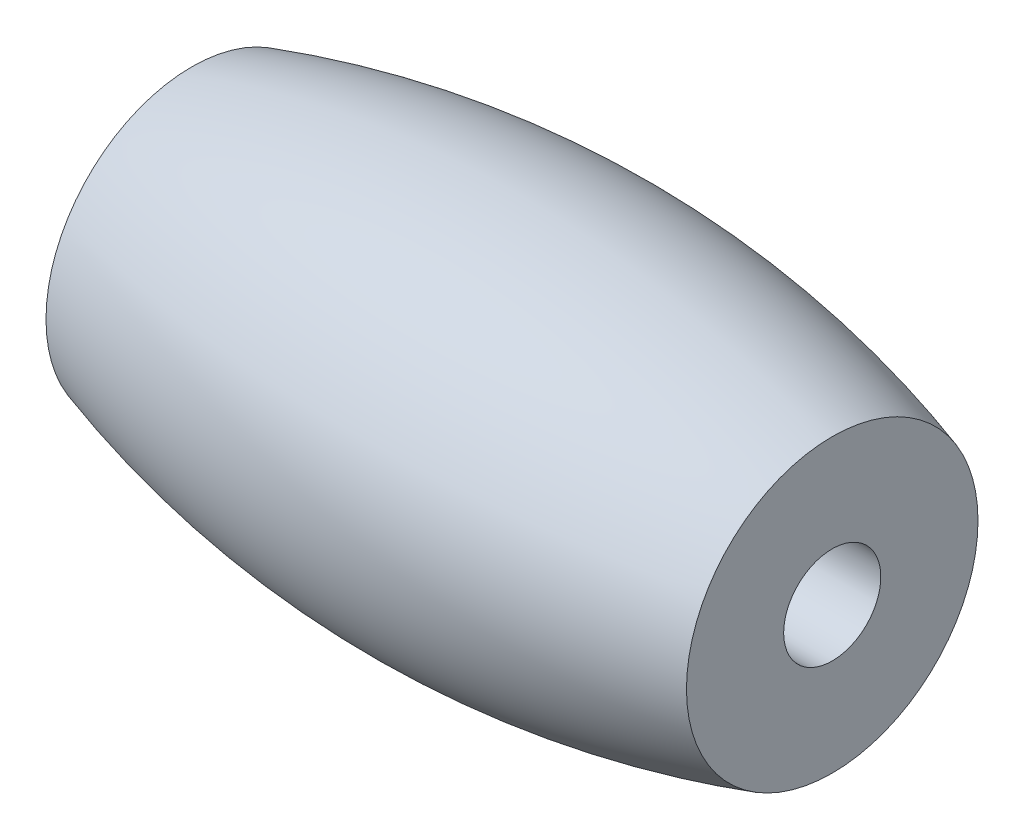
SolidWorks part; units mm, degrees
ref_plane "Front Plane" through (0, 0, 0) normal (0, 0, 1) x (1, 0, 0)
ref_plane "Top Plane" through (0, 0, 0) normal (0, 1, 0) x (1, 0, 0)
ref_plane "Right Plane" through (0, 0, 0) normal (1, 0, 0) x (0, 0, -1)
sketch "Sketch1" plane through (0, 0, 0) normal (0, 1, 0) x (1, 0, 0)
  line L0 (-19.2053, 0) -> (19.2053, 0)
  line L1 (-19.2053, 0) -> (-19.2053, -8.7417)
  line L2 (19.2053, 0) -> (19.2053, -8.7417)
  line L3 (0, 0) -> (0, -11.6556) construction
  arc A0 (19.2053, -8.7417) -> (-19.2053, -8.7417) centre (0, 53.0915) cw
  point P4 (0, 0)
  dimension "D2" = 64.7471
  dimension "D1" = 8.7417
  dimension "D3" = 38.4106
revolve "Revolve1" add sketch "Sketch1" angle 360 about L0
sketch "Sketch2" plane through (-19.2053, 0, 0) normal (-1, 0, 0) x (0, 0, 1)
  circle A0 centre (0, 0) radius 2.9139
  dimension "D1" = 5.8278
extrude "Cut-Extrude1" cut sketch "Sketch2" against normal through all
